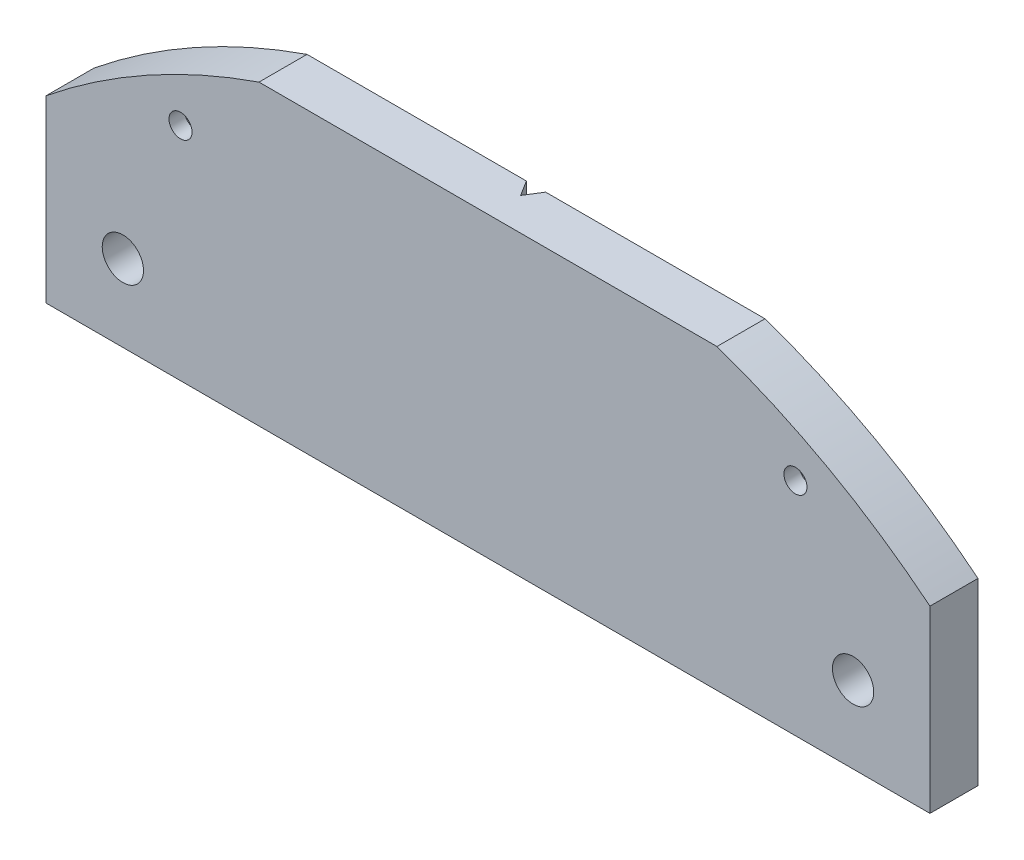
SolidWorks part; units mm, degrees
ref_plane "Front Plane" through (0, 0, 0) normal (0, 0, 1) x (1, 0, 0)
ref_plane "Top Plane" through (0, 0, 0) normal (0, 1, 0) x (1, 0, 0)
ref_plane "Right Plane" through (0, 0, 0) normal (1, 0, 0) x (0, 0, -1)
sketch "Sketch3" plane through (0, 0, 0) normal (0, 0, 1) x (1, 0, 0)
  line L1 (-46, 15.5) -> (46, 15.5)
  line L2 (-46, 15.5) -> (-46, -15.5)
  line L3 (-46, -15.5) -> (46, -15.5)
  line L4 (46, 15.5) -> (46, -15.5)
  line L5 (-46, 15.5) -> (46, -15.5) construction
  line L6 (-46, -15.5) -> (46, 15.5) construction
  point P0 (0, 0)
  dimension "D1" = 31
  dimension "D2" = 92
extrude "Boss-Extrude2" add sketch "Sketch3" along normal blind 5
sketch "Sketch4" plane through (0, 0, 5) normal (0, 0, 1) x (1, 0, 0)
  line L0 (-46, -15.5) -> (46, -15.5) construction
  circle A0 centre (0, -53.5) radius 73
  circle A1 centre (0, -53.5) radius 103
  dimension "D1" = 146
  dimension "D3" = 30
  dimension "D2" = 38
extrude "Cut-Extrude1" cut sketch "Sketch4" against normal through all
sketch "Sketch5" plane through (0, 0, 5) normal (0, 0, 1) x (1, 0, 0)
  line L1 (-46, -15.5) -> (46, -15.5) construction
  line L2 (46, -15.5) -> (46, 3.1833) construction
  line L3 (23.8328, 15.5) -> (-23.8328, 15.5) construction
  line L4 (0, -15.5) -> (0, 15.5) construction
  circle A0 centre (38, -7.5) radius 2.15
  circle A1 centre (-38, -7.5) radius 2.15
  dimension "D1" = 4.3
  dimension "D2" = 8
  dimension "D3" = 8
extrude "Cut-Extrude2" cut sketch "Sketch5" against normal through all
sketch "Sketch7" plane through (0, -15.5, 0) normal (0, -1, 0) x (1, 0, 0)
  line L0 (0, 0) -> (0, 5) construction
  line L1 (-46, 0) -> (46, 0) construction
  line L2 (-46, 5) -> (46, 5) construction
  line L3 (-1, 0) -> (0, 1.6)
  line L4 (0, 1.6) -> (1, 0)
  line L5 (1, 0) -> (-1, 0)
  dimension "D1" = 1
  dimension "D2" = 1
  dimension "D3" = 1.6
extrude "Cut-Extrude4" cut sketch "Sketch7" against normal through all
sketch "Sketch8" plane through (0, 0, 5) normal (0, 0, 1) x (1, 0, 0)
  line L0 (-46, -15.5) -> (46, -15.5) construction
  line L1 (-46, 3.1833) -> (-46, -15.5) construction
  line L2 (46, -15.5) -> (46, 3.1833) construction
  circle A0 centre (-32, 7.5) radius 1.2
  circle A1 centre (32, 7.5) radius 1.2
  dimension "D1" = 2.4
  dimension "D4" = 2.4
  dimension "D2" = 23
  dimension "D3" = 14
  dimension "D5" = 14
  dimension "D6" = 23
extrude "Cut-Extrude5" cut sketch "Sketch8" against normal through all
sketch "Sketch9" plane through (0, 0, 0) normal (0, 0, -1) x (-1, 0, 0)
  circle A0 centre (32, 7.5) radius 2.1
  circle A1 centre (-32, 7.5) radius 2.1
  dimension "D1" = 4.2
  dimension "D2" = 4.2
extrude "Cut-Extrude6" cut sketch "Sketch9" against normal blind 3.4
